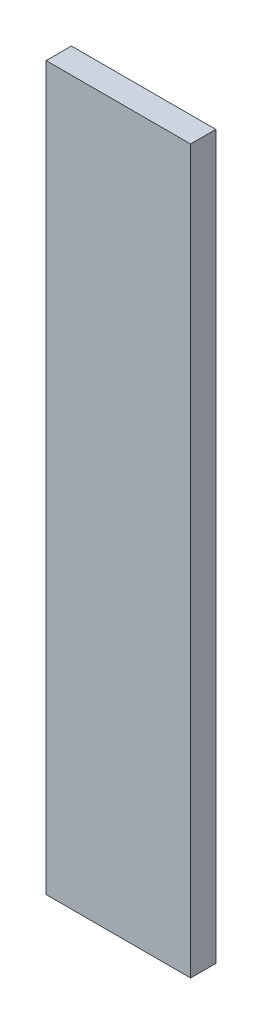
SolidWorks part; units mm, degrees
ref_plane "Front Plane" through (0, 0, 0) normal (0, 0, 1) x (1, 0, 0)
ref_plane "Top Plane" through (0, 0, 0) normal (0, 1, 0) x (1, 0, 0)
ref_plane "Right Plane" through (0, 0, 0) normal (1, 0, 0) x (0, 0, -1)
sketch "Sketch1" plane through (0, 0, 0) normal (0, 0, 1) x (1, 0, 0)
  line L1 (0, 0) -> (50.8, 0)
  line L2 (0, 0) -> (0, -254)
  line L3 (0, -254) -> (50.8, -254)
  line L4 (50.8, 0) -> (50.8, -254)
  dimension "D1" = 50.8
  dimension "D2" = 254
extrude "Boss-Extrude1" add sketch "Sketch1" along normal blind 8.89
sketch "Sketch2" plane through (0, 0, 0) normal (0, 1, 0) x (1, 0, 0)
  line L0 (25.4, 0) -> (25.4, -8.89) construction
  line L1 (50.8, 0) -> (0, 0) construction
  line L2 (50.8, -8.89) -> (0, -8.89) construction
